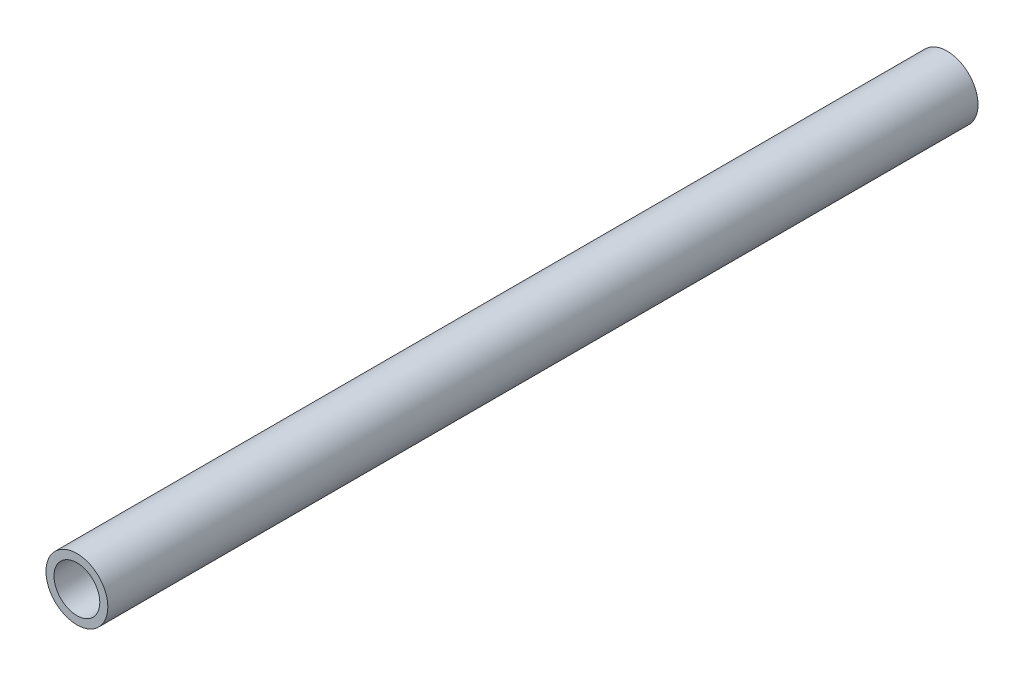
SolidWorks part; units mm, degrees
ref_plane "Front Plane" through (0, 0, 0) normal (0, 0, 1) x (1, 0, 0)
ref_plane "Top Plane" through (0, 0, 0) normal (0, 1, 0) x (1, 0, 0)
ref_plane "Right Plane" through (0, 0, 0) normal (1, 0, 0) x (0, 0, -1)
sketch "Sketch1" plane through (0, 0, 0) normal (0, 0, 1) x (1, 0, 0)
  circle A0 centre (0, 0) radius 10.668
  dimension "Pipe OD" = 21.336
extrude "Extrude-Thin1" add sketch "Sketch1" along normal mid plane 300 thin thin type one direction reverse wall 2.7686
